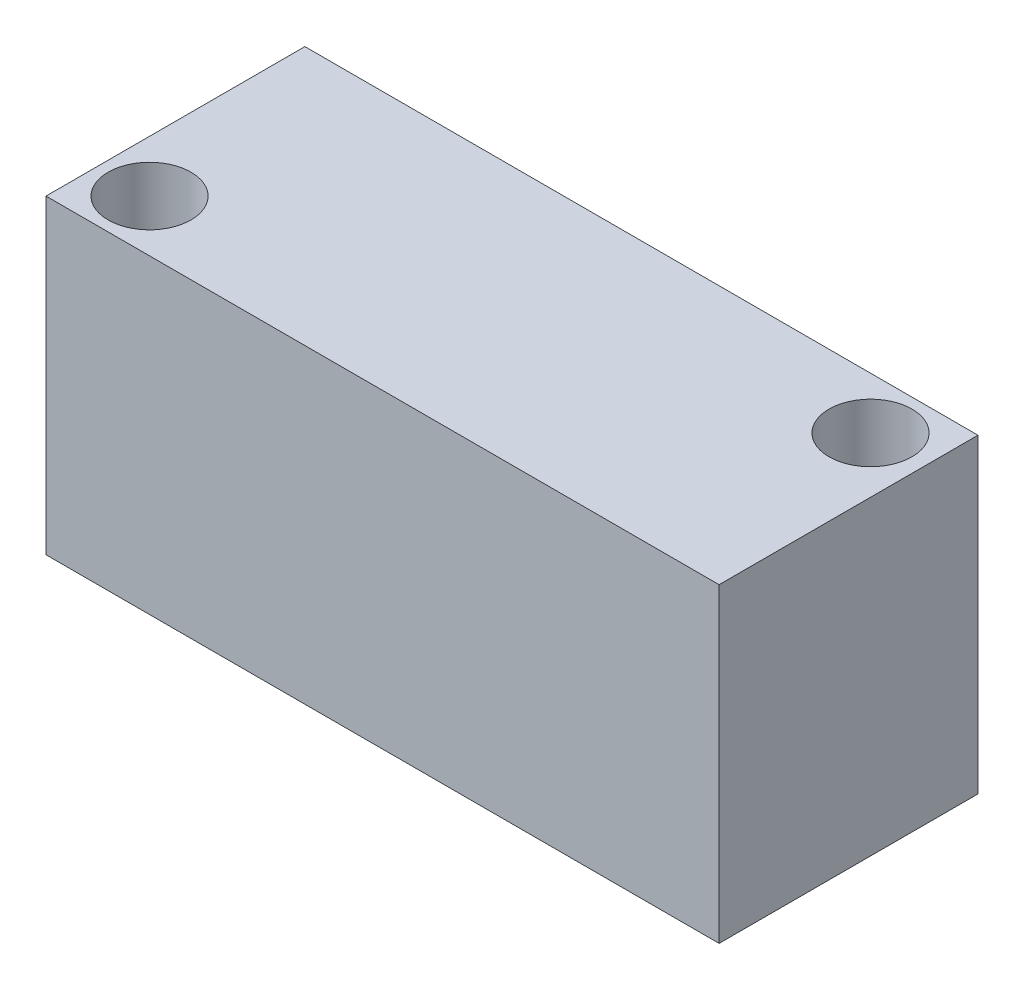
SolidWorks part; units mm, degrees
ref_plane "Front Plane" through (0, 0, 0) normal (0, 0, 1) x (1, 0, 0)
ref_plane "Top Plane" through (0, 0, 0) normal (0, 1, 0) x (1, 0, 0)
ref_plane "Right Plane" through (0, 0, 0) normal (1, 0, 0) x (0, 0, -1)
sketch "Sketch1" plane through (0, 0, 0) normal (0, 1, 0) x (1, 0, 0)
  line L0 (32.3146, 1.3131) -> (97.3146, 1.3131)
  line L1 (32.3146, 1.3131) -> (32.3146, -23.6869)
  line L2 (32.3146, -23.6869) -> (97.3146, -23.6869)
  line L3 (97.3146, 1.3131) -> (97.3146, -23.6869)
  line L4 (32.3146, 1.3131) -> (97.3146, -23.6869) construction
  line L5 (32.3146, -23.6869) -> (97.3146, 1.3131) construction
  circle A0 centre (37.3146, -18.6869) radius 4
  circle A1 centre (91.9344, -3.6869) radius 4
  point P0 (64.8146, -11.1869)
  dimension "D4" = 8
  dimension "D5" = 8
  dimension "D1" = 25
  dimension "D2" = 65
  dimension "D3" = 5
  dimension "D6" = 5
  dimension "D7" = 5
extrude "Boss-Extrude1" add sketch "Sketch1" along normal blind 30
